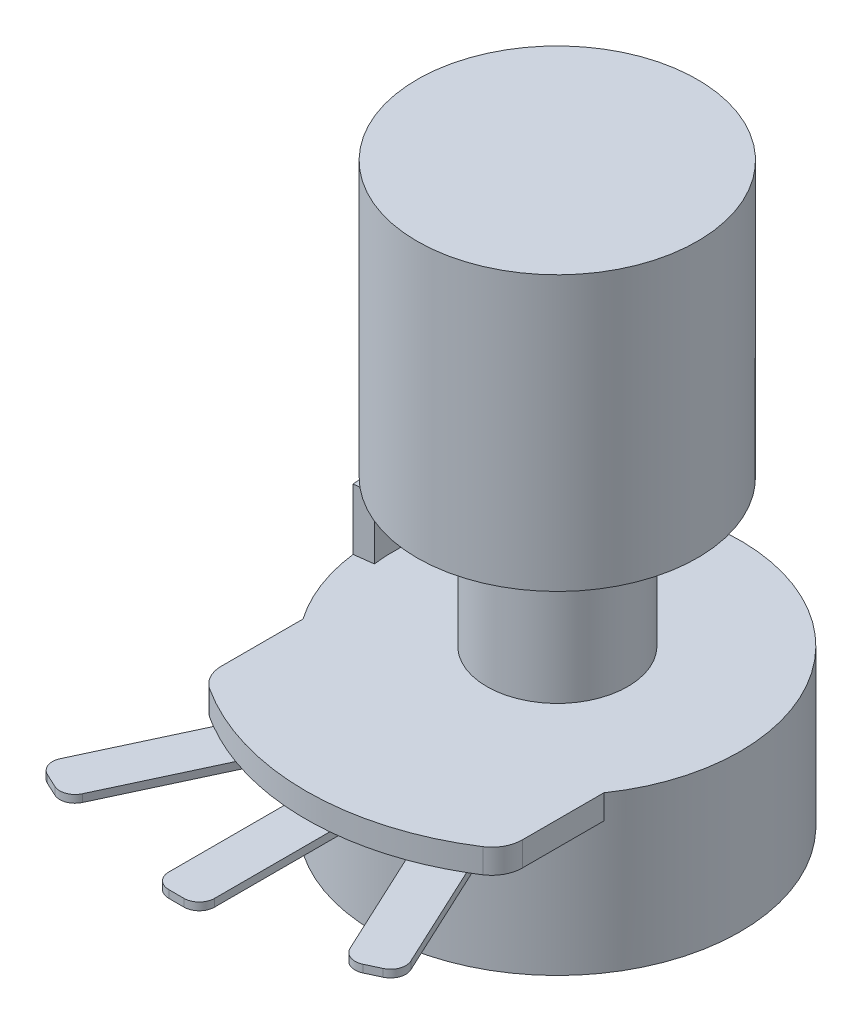
SolidWorks part; units mm, degrees
ref_plane "Front Plane" through (0, 0, 0) normal (0, 0, 1) x (1, 0, 0)
ref_plane "Top Plane" through (0, 0, 0) normal (0, 1, 0) x (1, 0, 0)
ref_plane "Right Plane" through (0, 0, 0) normal (1, 0, 0) x (0, 0, -1)
sketch "Sketch1" plane through (0, 0, 0) normal (0, 1, 0) x (1, 0, 0)
  circle A0 centre (0, 0) radius 12
  dimension "D1" = 24
extrude "Boss-Extrude1" add sketch "Sketch1" along normal blind 10.25
sketch "Sketch4" plane through (0, 10.25, 0) normal (0, 1, 0) x (1, 0, 0)
  line L0 (-1006.9252, 12) -> (48993.0748, 12) construction
  line L1 (9.875, -16.5) -> (-9.875, -16.5)
  line L2 (9.875, -16.5) -> (9.875, 0)
  line L3 (9.875, 0) -> (-9.875, 0)
  line L4 (-9.875, -16.5) -> (-9.875, 0)
  line L5 (9.875, -16.5) -> (-9.875, 0) construction
  line L6 (9.875, 0) -> (-9.875, -16.5) construction
  circle A0 centre (0, 0) radius 12 construction
  point P0 (0, -8.25)
  dimension "D1" = 19.75
  dimension "D2" = 28.5
extrude "Boss-Extrude4" add sketch "Sketch4" against normal blind 1.6
sketch "Sketch5" plane through (0, 10.25, 0) normal (0, 1, 0) x (1, 0, 0)
  circle A0 centre (0, 0) radius 16.5
extrude "Cut-Extrude1" cut sketch "Sketch5" against normal blind 1.6 flip side to cut
fillet "Fillet2" radius 2 2 edges at (9.875, 9.45, 13.2187) (-9.875, 9.45, 13.2187)
sketch "Sketch6" plane through (0, 8.65, 0) normal (0, -1, 0) x (1, 0, 0)
  line L0 (-1017.1879, 16.5) -> (48982.8121, 16.5) construction
  line L1 (1.5, 12.6758) -> (-1.5, 12.6758)
  line L2 (1.5, 12.6758) -> (1.5, 25)
  line L3 (1.5, 25) -> (-1.5, 25)
  line L4 (-1.5, 12.6758) -> (-1.5, 25)
  line L5 (1.5, 12.6758) -> (-1.5, 25) construction
  line L6 (1.5, 25) -> (-1.5, 12.6758) construction
  arc A0 (8.9612, 13.8545) -> (-8.9612, 13.8545) centre (0, 0) ccw construction
  point P0 (0, 18.8379)
  dimension "D1" = 3
  dimension "D2" = 8.5
extrude "Boss-Extrude6" add sketch "Sketch6" along normal blind 0.5
fillet "Fillet3" radius 1 2 edges at (1.5, 8.4, 25) (-1.5, 8.4, 25)
pattern_circular "CirPattern1" count 2 every 25 about axis through (0, 0, 0) along (0, 1, 0) of "Boss-Extrude6", "Fillet3"
pattern_circular "CirPattern2" count 2 every 25 about axis through (0, 0, 0) along (0, 1, 0) of "Boss-Extrude6", "Fillet3"
sketch "Sketch2" plane through (0, 10.25, 0) normal (0, 1, 0) x (1, 0, 0)
  circle A0 centre (0, 0) radius 4.625
  dimension "D1" = 9.25
extrude "Boss-Extrude2" add sketch "Sketch2" along normal blind 9.6
sketch "Sketch3" plane through (0, 19.85, 0) normal (0, 1, 0) x (1, 0, 0)
  circle A0 centre (0, 0) radius 9.2
  dimension "D1" = 18.4
extrude "Boss-Extrude3" add sketch "Sketch3" along normal blind 18
sketch "Sketch7" plane through (0, 10.25, 0) normal (0, 1, 0) x (1, 0, 0)
  line L0 (0, 0) -> (-11.9059, 1.5) construction
  line L1 (0, 0) -> (-11.9059, -1.5) construction
  line L2 (-1000, 0) -> (49000, 0) construction
  line L3 (-11.9059, 1.5) -> (-10.6657, 1.3438)
  line L4 (-10.6657, -1.3438) -> (-11.9059, -1.5)
  arc A0 (-11.9059, -1.5) -> (-11.9059, 1.5) centre (0, 0) cw
  arc A1 (9.875, -6.8179) -> (-9.875, -6.8179) centre (0, 0) ccw construction
  arc A2 (-10.6657, -1.3438) -> (-10.6657, 1.3438) centre (0, 0) cw
  dimension "D1" = 3
  dimension "D2" = 1.25
extrude "Boss-Extrude7" add sketch "Sketch7" along normal blind 4
